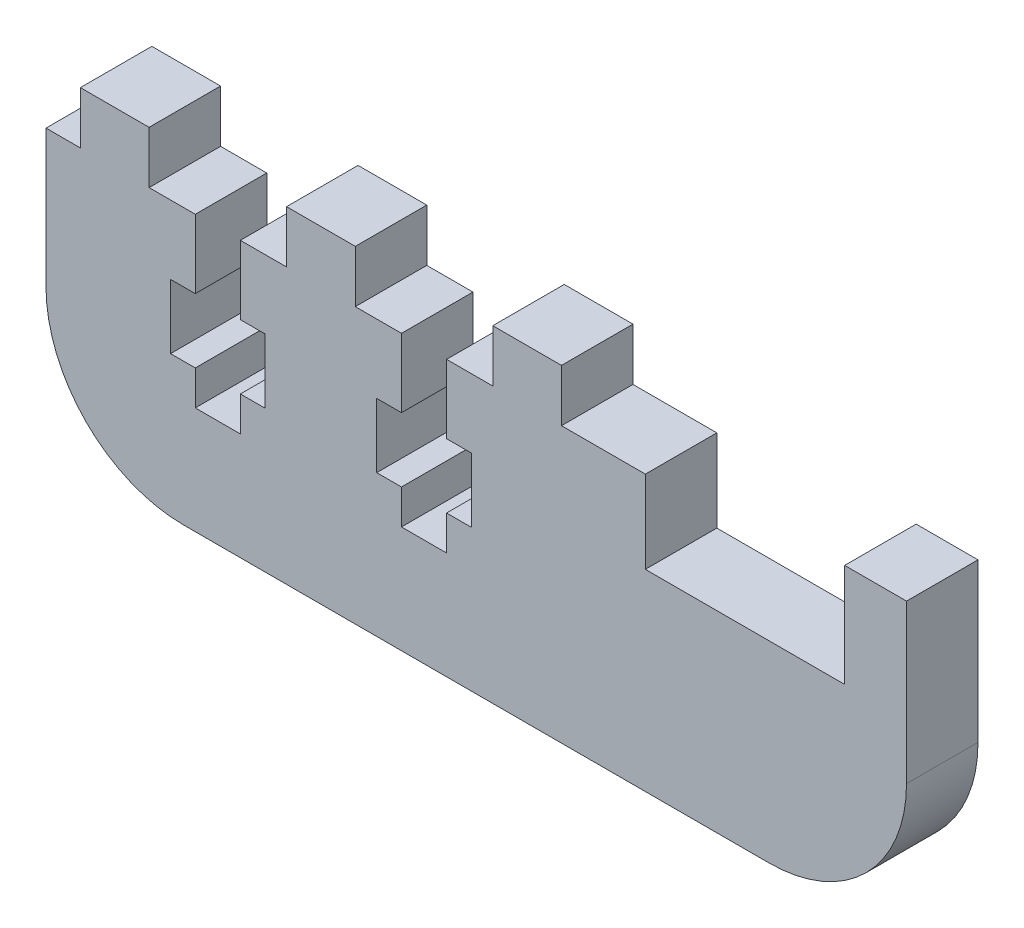
SolidWorks part; units mm, degrees
material "Acrylic (Blue)"
ref_plane "Front Plane" through (0, 0, 0) normal (0, 0, 1) x (1, 0, 0)
ref_plane "Top Plane" through (0, 0, 0) normal (0, 1, 0) x (1, 0, 0)
ref_plane "Right Plane" through (0, 0, 0) normal (1, 0, 0) x (0, 0, -1)
sketch "Sketch1" plane through (0, 0, 0) normal (0, 0, 1) x (1, 0, 0)
  line L1 (12.7, 0) -> (-12.7, 0) construction
  line L2 (12.7, 0) -> (12.7, 3.175) construction
  line L3 (12.7, 3.175) -> (-12.7, 3.175) construction
  line L4 (-12.7, 0) -> (-12.7, 3.175) construction
  line L5 (-12.827, 3.175) -> (-89.027, 3.175) construction
  line L6 (-12.827, 3.175) -> (-12.827, -1.905) construction
  line L7 (-12.827, -1.905) -> (-89.027, -1.905) construction
  line L8 (-89.027, 3.175) -> (-89.027, -1.905) construction
  line L9 (12.827, 3.175) -> (89.027, 3.175) construction
  line L10 (12.827, 3.175) -> (12.827, -1.905) construction
  line L11 (12.827, -1.905) -> (89.027, -1.905) construction
  line L12 (89.027, 3.175) -> (89.027, -1.905) construction
  line L13 (12.7, 3.175) -> (12.827, 3.175) construction
  line L14 (-12.7, 3.175) -> (-12.827, 3.175) construction
  line L16 (-11.43, -1.905) -> (-11.43, -9.525)
  line L17 (-11.43, -9.525) -> (6.985, -9.525)
  line L18 (12.7, 0) -> (6.985, 0)
  line L19 (-11.43, -1.905) -> (-12.827, -1.905)
  line L21 (-12.827, -1.905) -> (-66.802, -1.905)
  line L22 (-66.802, -1.905) -> (-66.802, -27.305)
  line L23 (-66.802, -27.305) -> (12.7, -27.305)
  line L24 (12.7, 0) -> (12.7, -27.305)
  line L26 (6.985, 0) -> (6.985, -9.525)
  line B0 (-53.0098, -1.905) -> (-53.0098, -8.255) construction
  line B1 (-53.0098, -8.255) -> (-55.2958, -8.255) construction
  line B2 (-55.2958, -8.255) -> (-55.2958, -14.1986) construction
  line B3 (-55.2958, -14.1986) -> (-53.0098, -14.1986) construction
  line B4 (-53.0098, -14.1986) -> (-53.0098, -17.399) construction
  line B5 (-53.0098, -17.399) -> (-48.8442, -17.399) construction
  line B6 (-48.8442, -17.399) -> (-48.8442, -14.1986) construction
  line B7 (-48.8442, -14.1986) -> (-46.5582, -14.1986) construction
  line B8 (-46.5582, -14.1986) -> (-46.5582, -8.255) construction
  line B9 (-46.5582, -8.255) -> (-48.8442, -8.255) construction
  line B10 (-48.8442, -8.255) -> (-48.8442, -1.905) construction
  line B11 (-48.8442, -1.905) -> (-44.577, -1.905) construction
  line B12 (-44.577, -1.905) -> (-44.577, 2.921) construction
  line B13 (-44.577, 2.921) -> (-38.227, 2.921) construction
  line B14 (-38.227, 2.921) -> (-38.227, -1.905) construction
  line B15 (-53.0098, -1.905) -> (-57.277, -1.905) construction
  line B16 (-57.277, -1.905) -> (-57.277, 2.921) construction
  line B17 (-57.277, 2.921) -> (-63.627, 2.921) construction
  line B18 (-63.627, 2.921) -> (-63.627, -1.905) construction
  line B19 (-48.8442, -1.905) -> (-53.0098, -1.905) construction
  line B20 (-19.177, 2.921) -> (-19.177, -1.905) construction
  line B21 (-33.9598, -1.905) -> (-33.9598, -8.255) construction
  line B22 (-33.9598, -8.255) -> (-36.2458, -8.255) construction
  line B23 (-36.2458, -8.255) -> (-36.2458, -14.1986) construction
  line B24 (-36.2458, -14.1986) -> (-33.9598, -14.1986) construction
  line B25 (-33.9598, -14.1986) -> (-33.9598, -17.399) construction
  line B26 (-33.9598, -17.399) -> (-29.7942, -17.399) construction
  line B27 (-29.7942, -17.399) -> (-29.7942, -14.1986) construction
  line B28 (-29.7942, -14.1986) -> (-27.5082, -14.1986) construction
  line B29 (-27.5082, -14.1986) -> (-27.5082, -8.255) construction
  line B30 (-27.5082, -8.255) -> (-29.7942, -8.255) construction
  line B31 (-29.7942, -8.255) -> (-29.7942, -1.905) construction
  line B32 (-29.7942, -1.905) -> (-25.527, -1.905) construction
  line B33 (-25.527, -1.905) -> (-25.527, 2.921) construction
  line B34 (-25.527, 2.921) -> (-19.177, 2.921) construction
  line B35 (-33.9598, -1.905) -> (-38.227, -1.905) construction
  line B36 (-38.227, -1.905) -> (-38.227, 2.921) construction
  line B37 (-38.227, 2.921) -> (-44.577, 2.921) construction
  line B38 (-44.577, 2.921) -> (-44.577, -1.905) construction
  line B39 (-29.7942, -1.905) -> (-33.9598, -1.905) construction
  dimension "D1" = 3.175
  dimension "D2" = 25.654
  dimension "D3" = 25.4
  dimension "D4" = 5.08
  dimension "D5" = 76.2
  dimension "D6" = 18.415
  dimension "D7" = 9.525
  dimension "D8" = 5.715
  dimension "D9" = 25.4
  dimension "D10" = 6.35
  dimension "D11" = 3.175
  dimension "D12" = 79.502
sketch_block_instance "NUT_HOLE_2X-1"
sketch_block "NUT_HOLE_2X" parameters "D1"=6.35, "D2"=4.1656, "D3"=25.4, "D4"=4.826, "D5"=8.7376, "D6"=5.9436, "D7"=6.35, "D8"=20.32, "D9"=2
extrude "Boss-Extrude1" add sketch "Sketch1" along normal blind 6.604
fillet "Fillet1" radius 12.7 2 edges at (-66.802, -27.305, 3.302) (12.7, -27.305, 3.302)
sketch "Sketch2" plane through (0, 0, 6.604) normal (0, 0, 1) x (1, 0, 0)
  line L0 (-53.0098, -1.905) -> (-53.0098, -8.255) construction
  line L1 (-53.0098, -8.255) -> (-55.2958, -8.255) construction
  line L2 (-55.2958, -8.255) -> (-55.2958, -14.1986) construction
  line L3 (-55.2958, -14.1986) -> (-53.0098, -14.1986) construction
  line L4 (-53.0098, -14.1986) -> (-53.0098, -17.399) construction
  line L5 (-53.0098, -17.399) -> (-48.8442, -17.399) construction
  line L6 (-48.8442, -14.1986) -> (-46.5582, -14.1986) construction
  line L7 (-48.8442, -17.399) -> (-48.8442, -14.1986) construction
  line L8 (-46.5582, -14.1986) -> (-46.5582, -8.255) construction
  line L9 (-46.5582, -8.255) -> (-48.8442, -8.255) construction
  line L10 (-48.8442, -8.255) -> (-48.8442, -1.905) construction
  line L11 (-33.9598, -1.905) -> (-33.9598, -8.255) construction
  line L12 (-27.5082, -8.255) -> (-29.7942, -8.255) construction
  line L13 (-27.5082, -14.1986) -> (-27.5082, -8.255) construction
  line L14 (-29.7942, -14.1986) -> (-27.5082, -14.1986) construction
  line L15 (-33.9598, -17.399) -> (-29.7942, -17.399) construction
  line L16 (-29.7942, -17.399) -> (-29.7942, -14.1986) construction
  line L17 (-33.9598, -14.1986) -> (-33.9598, -17.399) construction
  line L18 (-36.2458, -14.1986) -> (-33.9598, -14.1986) construction
  line L19 (-36.2458, -8.255) -> (-36.2458, -14.1986) construction
  line L20 (-33.9598, -8.255) -> (-36.2458, -8.255) construction
  line L21 (-29.7942, -8.255) -> (-29.7942, -1.905) construction
  line L22 (-53.0098, -1.905) -> (-53.0098, -8.255)
  line L23 (-53.0098, -8.255) -> (-55.2958, -8.255)
  line L24 (-55.2958, -8.255) -> (-55.2958, -14.1986)
  line L25 (-55.2958, -14.1986) -> (-53.0098, -14.1986)
  line L26 (-53.0098, -14.1986) -> (-53.0098, -17.399)
  line L27 (-53.0098, -17.399) -> (-48.8442, -17.399)
  line L28 (-48.8442, -14.1986) -> (-46.5582, -14.1986)
  line L29 (-48.8442, -17.399) -> (-48.8442, -14.1986)
  line L30 (-46.5582, -14.1986) -> (-46.5582, -8.255)
  line L31 (-46.5582, -8.255) -> (-48.8442, -8.255)
  line L32 (-48.8442, -8.255) -> (-48.8442, -1.905)
  line L33 (-33.9598, -1.905) -> (-33.9598, -8.255)
  line L34 (-27.5082, -8.255) -> (-29.7942, -8.255)
  line L35 (-27.5082, -14.1986) -> (-27.5082, -8.255)
  line L36 (-29.7942, -14.1986) -> (-27.5082, -14.1986)
  line L37 (-33.9598, -17.399) -> (-29.7942, -17.399)
  line L38 (-29.7942, -17.399) -> (-29.7942, -14.1986)
  line L39 (-33.9598, -14.1986) -> (-33.9598, -17.399)
  line L40 (-36.2458, -14.1986) -> (-33.9598, -14.1986)
  line L41 (-36.2458, -8.255) -> (-36.2458, -14.1986)
  line L42 (-33.9598, -8.255) -> (-36.2458, -8.255)
  line L43 (-29.7942, -8.255) -> (-29.7942, -1.905)
  line L44 (-53.0098, -1.905) -> (-48.8442, -1.905)
  line L45 (-33.9598, -1.905) -> (-29.7942, -1.905)
extrude "Cut-Extrude1" cut sketch "Sketch2" against normal through all
sketch "Sketch3" plane through (0, 0, 6.604) normal (0, 0, 1) x (1, 0, 0)
  line L0 (-63.627, 2.921) -> (-63.627, -1.905) construction
  line L1 (-57.277, 2.921) -> (-63.627, 2.921) construction
  line L2 (-57.277, -1.905) -> (-57.277, 2.921) construction
  line L3 (-44.577, -1.905) -> (-44.577, 2.921) construction
  line L4 (-44.577, 2.921) -> (-38.227, 2.921) construction
  line L5 (-38.227, 2.921) -> (-38.227, -1.905) construction
  line L6 (-25.527, -1.905) -> (-25.527, 2.921) construction
  line L7 (-25.527, 2.921) -> (-19.177, 2.921) construction
  line L8 (-19.177, 2.921) -> (-19.177, -1.905) construction
  line L9 (-63.627, 2.921) -> (-63.627, -1.905)
  line L10 (-57.277, 2.921) -> (-63.627, 2.921)
  line L11 (-57.277, -1.905) -> (-57.277, 2.921)
  line L12 (-44.577, -1.905) -> (-44.577, 2.921)
  line L13 (-44.577, 2.921) -> (-38.227, 2.921)
  line L14 (-38.227, 2.921) -> (-38.227, -1.905)
  line L15 (-25.527, -1.905) -> (-25.527, 2.921)
  line L16 (-25.527, 2.921) -> (-19.177, 2.921)
  line L17 (-19.177, 2.921) -> (-19.177, -1.905)
  line L18 (-63.627, -1.905) -> (-57.277, -1.905)
  line L19 (-44.577, -1.905) -> (-38.227, -1.905)
  line L20 (-25.527, -1.905) -> (-19.177, -1.905)
extrude "Boss-Extrude2" add sketch "Sketch3" against normal up to surface (6.604 mm away) up to face at (-34.2601, -10.8466, 0)
other "Move Face1" [suppressed] parameters "D1"=0.0508
